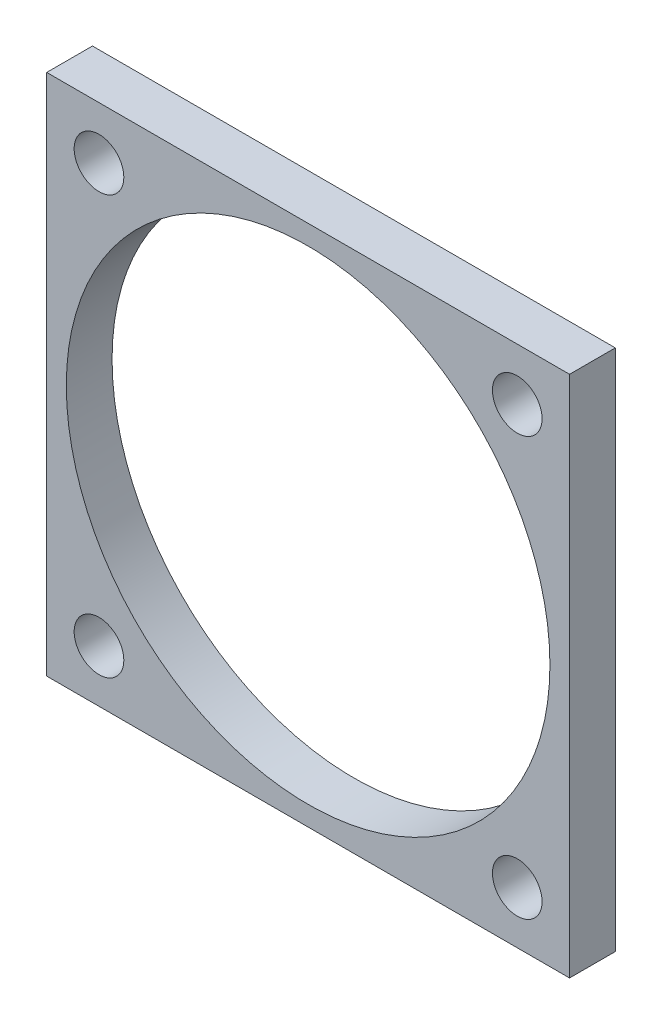
SolidWorks part; units mm, degrees
ref_plane "Front Plane" through (0, 0, 0) normal (0, 0, 1) x (1, 0, 0)
ref_plane "Top Plane" through (0, 0, 0) normal (0, 1, 0) x (1, 0, 0)
ref_plane "Right Plane" through (0, 0, 0) normal (1, 0, 0) x (0, 0, -1)
sketch "Sketch1" plane through (0, 0, 0) normal (0, 0, 1) x (1, 0, 0)
  line L1 (0, 0) -> (40, 0)
  line L2 (0, 0) -> (0, -40)
  line L3 (0, -40) -> (40, -40)
  line L4 (40, 0) -> (40, -40)
  circle A0 centre (4, -4) radius 1.9
  circle A1 centre (36, -4) radius 1.9
  circle A2 centre (36, -36) radius 1.9
  circle A3 centre (4, -36) radius 1.9
  circle A4 centre (20, -20) radius 18.5
  dimension "D3" = 4
  dimension "D5" = 4
  dimension "D6" = 4
  dimension "D1" = 40
  dimension "D2" = 40
  dimension "D4" = 4
extrude "Boss-Extrude1" add sketch "Sketch1" along normal blind 3.5
